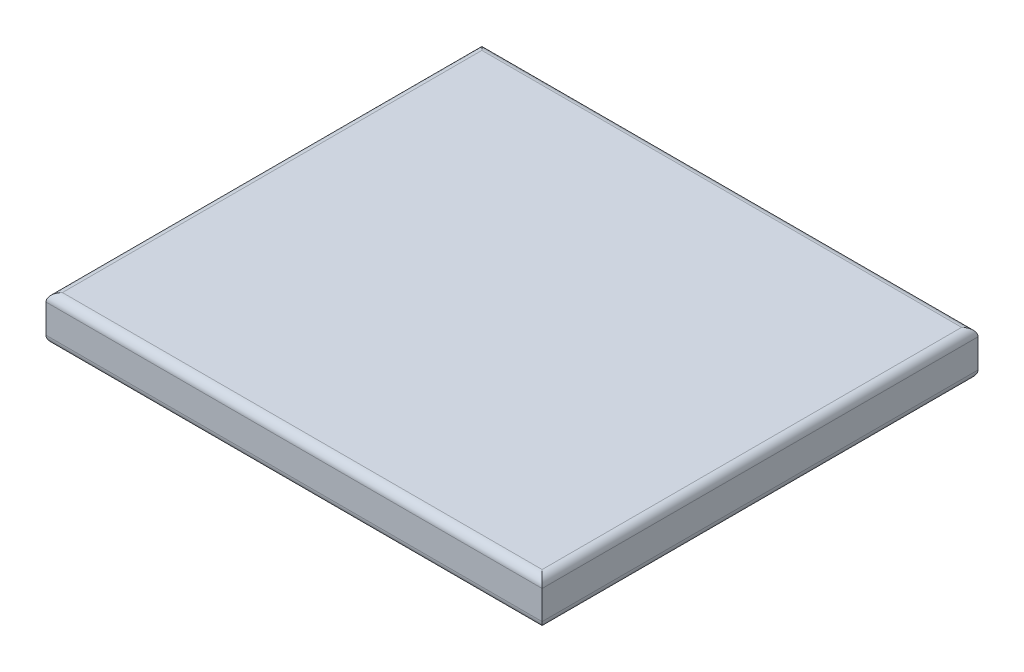
SolidWorks part; units mm, degrees
ref_plane "Front Plane" through (0, 0, 0) normal (0, 0, 1) x (1, 0, 0)
ref_plane "Top Plane" through (0, 0, 0) normal (0, 1, 0) x (1, 0, 0)
ref_plane "Right Plane" through (0, 0, 0) normal (1, 0, 0) x (0, 0, -1)
sketch "Sketch1" plane through (0, 0, 0) normal (0, 1, 0) x (1, 0, 0)
  line L1 (0, 0) -> (60.5, 0)
  line L2 (0, 0) -> (0, 53.15)
  line L3 (0, 53.15) -> (60.5, 53.15)
  line L4 (60.5, 0) -> (60.5, 53.15)
  dimension "D1" = 53.15
  dimension "D2" = 60.5
extrude "Boss-Extrude1" add sketch "Sketch1" along normal blind 5.5
fillet "Fillet1" radius 1 8 edges at (30.25, 0, 0) (60.5, 0, -26.575) (30.25, 0, -53.15) (0, 0, -26.575) (30.25, 5.5, -53.15) (60.5, 5.5, -26.575) (30.25, 5.5, 0) (0, 5.5, -26.575)
